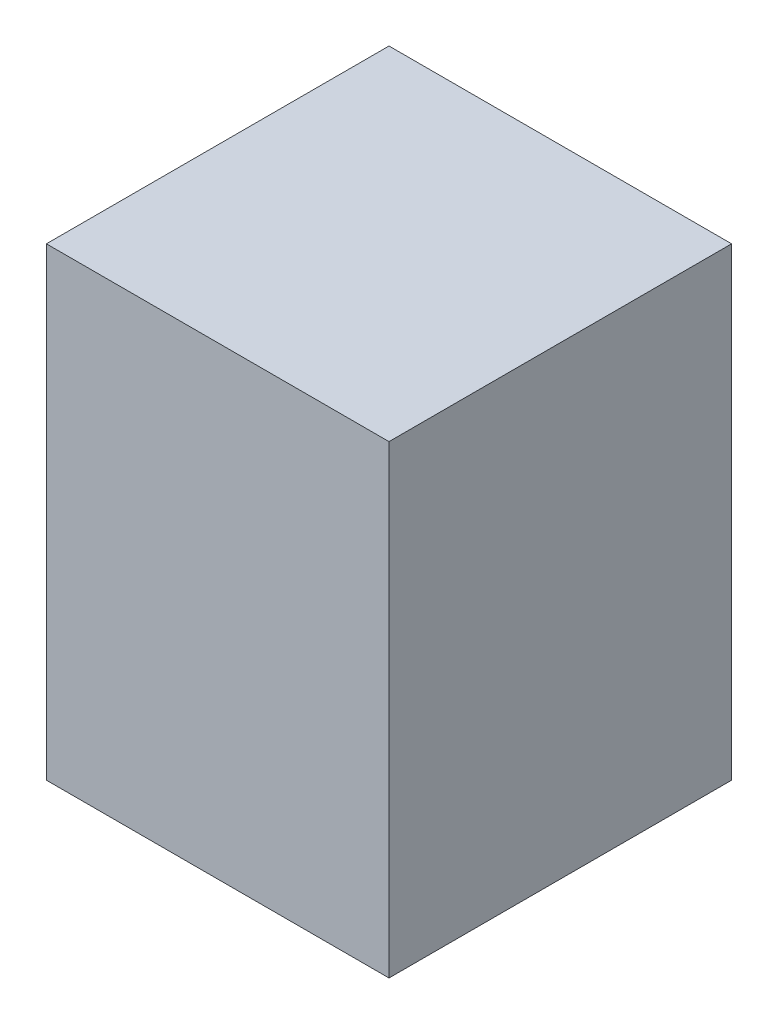
SolidWorks part; units mm, degrees
ref_plane "Front Plane" through (0, 0, 0) normal (0, 0, 1) x (1, 0, 0)
ref_plane "Top Plane" through (0, 0, 0) normal (0, 1, 0) x (1, 0, 0)
ref_plane "Right Plane" through (0, 0, 0) normal (1, 0, 0) x (0, 0, -1)
sketch "Sketch1" plane through (0, 0, 0) normal (0, 1, 0) x (1, 0, 0)
  line L1 (7.375, -7.375) -> (-7.375, -7.375)
  line L2 (7.375, -7.375) -> (7.375, 7.375)
  line L3 (7.375, 7.375) -> (-7.375, 7.375)
  line L4 (-7.375, -7.375) -> (-7.375, 7.375)
  line L5 (7.375, -7.375) -> (-7.375, 7.375) construction
  line L6 (7.375, 7.375) -> (-7.375, -7.375) construction
  point P0 (0, 0)
  dimension "D1" = 14.75
extrude "Boss-Extrude1" add sketch "Sketch1" along normal blind 20
